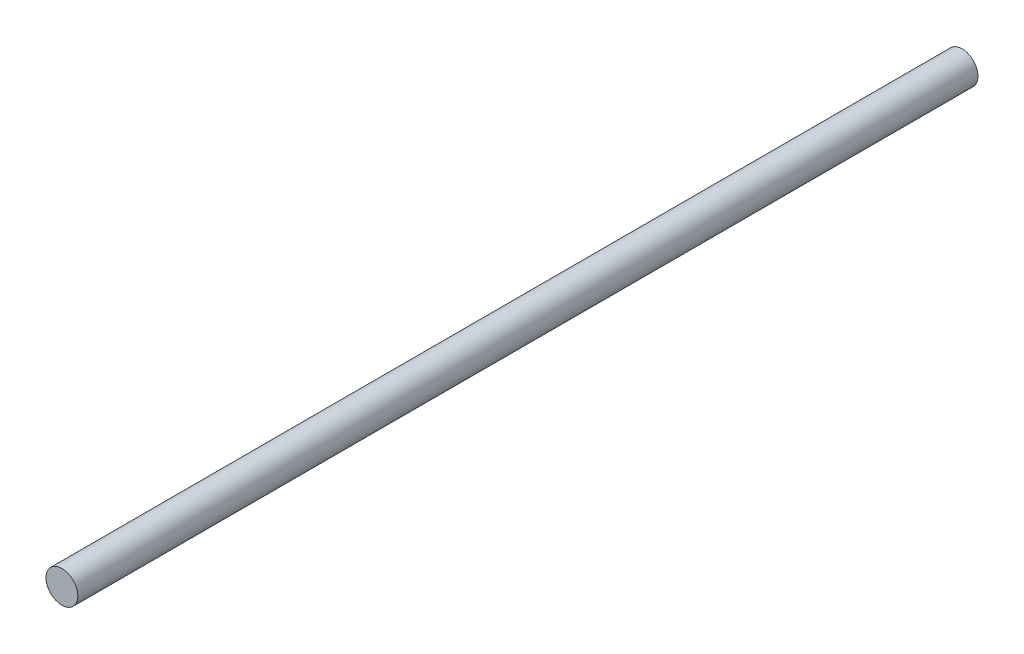
SolidWorks part; units mm, degrees
material "Balsa"
ref_plane "Front Plane" through (0, 0, 0) normal (0, 0, 1) x (1, 0, 0)
ref_plane "Top Plane" through (0, 0, 0) normal (0, 1, 0) x (1, 0, 0)
ref_plane "Right Plane" through (0, 0, 0) normal (1, 0, 0) x (0, 0, -1)
sketch "Sketch1" plane through (0, 0, 0) normal (0, 0, 1) x (1, 0, 0)
  circle A0 centre (0, 0) radius 6.5
  dimension "D1" = 13
extrude "Boss-Extrude1" add sketch "Sketch1" along normal blind 367.475 contours A0
